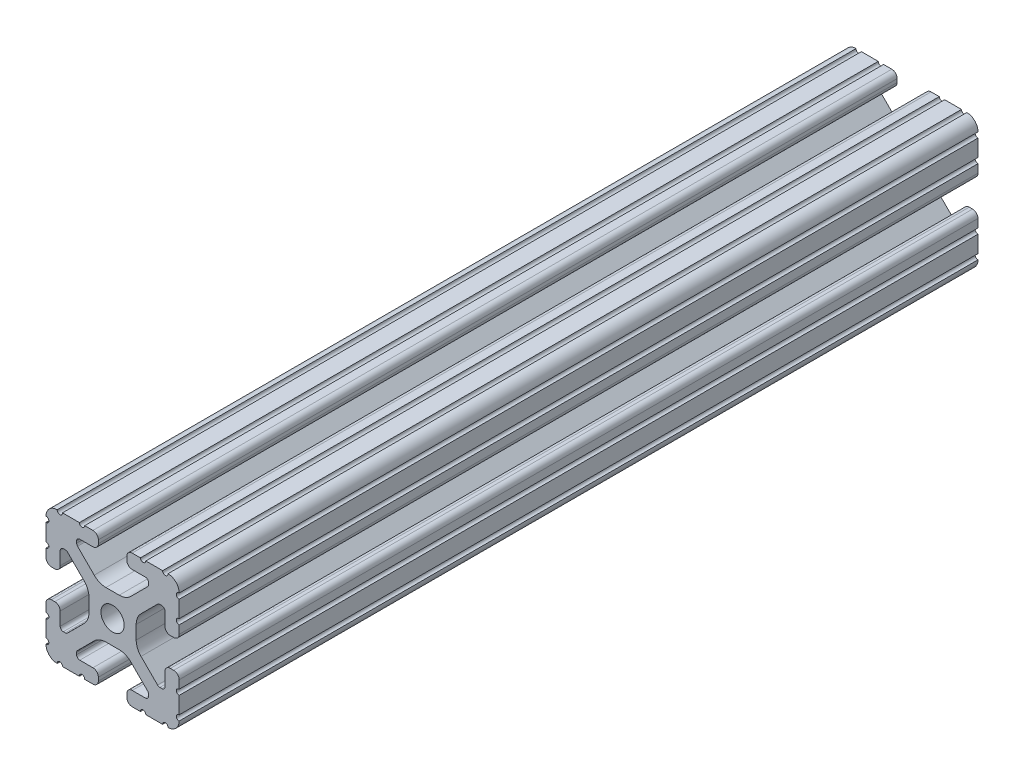
SolidWorks part; units mm, degrees
ref_plane "Front Plane" through (0, 0, 0) normal (0, 0, 1) x (1, 0, 0)
ref_plane "Top Plane" through (0, 0, 0) normal (0, 1, 0) x (1, 0, 0)
ref_plane "Right Plane" through (0, 0, 0) normal (1, 0, 0) x (0, 0, -1)
sketch "Sketch1" plane through (0, 0, 0) normal (0, 0, 1) x (1, 0, 0)
  line L0 (-4.064, 19.05) -> (-4.064, -19.05) construction
  line L1 (-19.05, -19.05) -> (19.05, -19.05) construction
  line L2 (-19.05, -19.05) -> (-19.05, 19.05) construction
  line L3 (-19.05, 19.05) -> (19.05, 19.05) construction
  line L4 (19.05, -19.05) -> (19.05, 19.05) construction
  line L5 (0, 19.05) -> (0, -19.05) construction
  line L6 (-19.05, 0) -> (19.05, 0) construction
  line L7 (-4.064, -19.05) -> (4.064, 19.05) construction
  line L8 (4.064, 19.05) -> (4.064, -19.05) construction
  circle A0 centre (0, 0) radius 3.3274
  point P0 (0, 0)
  line B0 (-10.287, 13.5524) -> (-10.287, 14.0843)
  line B1 (-9.3853, 14.986) -> (-5.6176, 14.986)
  line B2 (-4.064, 16.5396) -> (-4.064, 17.4964)
  line B3 (-5.6176, 19.05) -> (-7.9742, 19.05)
  line B4 (-9.4982, 19.05) -> (-14.3277, 19.05)
  line B5 (-19.05, 14.3277) -> (-19.05, 9.4961)
  line B6 (-19.05, 7.9763) -> (-19.05, 5.6176)
  line B7 (-17.4964, 4.064) -> (-16.5396, 4.064)
  line B8 (-14.986, 5.6176) -> (-14.986, 9.3853)
  line B9 (-14.0843, 10.287) -> (-13.516, 10.287)
  line B10 (-12.8784, 10.0229) -> (-8.1476, 5.2921)
  line B11 (-6.7564, 1.9335) -> (-6.7564, -1.9335)
  line B12 (-8.1476, -5.2921) -> (-12.8784, -10.0229)
  line B13 (-13.516, -10.287) -> (-14.0843, -10.287)
  line B14 (-14.986, -9.3853) -> (-14.986, -5.6176)
  line B15 (-16.5396, -4.064) -> (-17.4964, -4.064)
  line B16 (-19.05, -5.6176) -> (-19.05, -7.9763)
  line B17 (-19.05, -9.4961) -> (-19.05, -14.3277)
  line B18 (-14.3277, -19.05) -> (-9.4961, -19.05)
  line B19 (-7.9763, -19.05) -> (-5.6176, -19.05)
  line B20 (-4.064, -17.4964) -> (-4.064, -16.5396)
  line B21 (-5.6176, -14.986) -> (-9.3853, -14.986)
  line B22 (-10.287, -14.0843) -> (-10.287, -13.5524)
  line B23 (-10.0229, -12.9148) -> (-5.2522, -8.144)
  line B24 (-1.9022, -6.7564) -> (1.9022, -6.7564)
  line B25 (5.2522, -8.144) -> (10.0229, -12.9148)
  line B26 (10.287, -13.5524) -> (10.287, -14.0843)
  line B27 (9.3853, -14.986) -> (5.6176, -14.986)
  line B28 (4.064, -16.5396) -> (4.064, -17.4964)
  line B29 (5.6176, -19.05) -> (7.9763, -19.05)
  line B30 (9.4961, -19.05) -> (14.3277, -19.05)
  line B31 (19.05, -14.3277) -> (19.05, -9.4961)
  line B32 (19.05, -7.9763) -> (19.05, -5.6176)
  line B33 (17.4964, -4.064) -> (16.5396, -4.064)
  line B34 (14.986, -5.6176) -> (14.986, -9.3853)
  line B35 (14.0843, -10.287) -> (13.516, -10.287)
  line B36 (12.8784, -10.0229) -> (8.1476, -5.2921)
  line B37 (6.7564, -1.9335) -> (6.7564, 1.9335)
  line B38 (8.1476, 5.2921) -> (12.8784, 10.0229)
  line B39 (13.516, 10.287) -> (14.0843, 10.287)
  line B40 (14.986, 9.3853) -> (14.986, 5.6176)
  line B41 (16.5396, 4.064) -> (17.4964, 4.064)
  line B42 (19.05, 5.6176) -> (19.05, 7.9763)
  line B43 (19.05, 9.4961) -> (19.05, 14.3277)
  line B44 (14.3277, 19.05) -> (9.4982, 19.05)
  line B45 (7.9742, 19.05) -> (5.6176, 19.05)
  line B46 (4.064, 17.4964) -> (4.064, 16.5396)
  line B47 (5.6176, 14.986) -> (9.3853, 14.986)
  line B48 (10.287, 14.0843) -> (10.287, 13.5524)
  line B49 (10.0229, 12.9148) -> (5.2522, 8.144)
  line B50 (1.9022, 6.7564) -> (-1.9022, 6.7564)
  line B51 (-5.2522, 8.144) -> (-10.0229, 12.9148)
  circle B52 centre (0, 0) radius 3.3274
  arc B53 (-5.6176, 14.986) -> (-4.064, 16.5396) centre (-5.6176, 16.5396) ccw
  arc B54 (-4.064, 17.4964) -> (-5.6176, 19.05) centre (-5.6176, 17.4964) ccw
  arc B55 (-9.4982, 19.05) -> (-7.9742, 19.05) centre (-8.7362, 19.05) ccw
  arc B56 (-15.8475, 19.05) -> (-14.3277, 19.05) centre (-15.0876, 18.9933) ccw
  arc B57 (-15.8475, 19.05) -> (-19.05, 15.8475) centre (-15.8751, 15.8751) ccw
  arc B58 (-19.05, 14.3277) -> (-19.05, 15.8475) centre (-18.9933, 15.0876) ccw
  arc B59 (-19.05, 7.9763) -> (-19.05, 9.4961) centre (-18.9933, 8.7362) ccw
  arc B60 (-19.05, 5.6176) -> (-17.4964, 4.064) centre (-17.4964, 5.6176) ccw
  arc B61 (-16.5396, 4.064) -> (-14.986, 5.6176) centre (-16.5396, 5.6176) ccw
  arc B62 (-14.0843, 10.287) -> (-14.986, 9.3853) centre (-14.0843, 9.3853) ccw
  arc B63 (-12.8784, 10.0229) -> (-13.516, 10.287) centre (-13.516, 9.3853) ccw
  arc B64 (-6.7564, 1.9335) -> (-8.1476, 5.2921) centre (-11.5062, 1.9335) ccw
  arc B65 (-8.1476, -5.2921) -> (-6.7564, -1.9335) centre (-11.5062, -1.9335) ccw
  arc B66 (-13.516, -10.287) -> (-12.8784, -10.0229) centre (-13.516, -9.3853) ccw
  arc B67 (-14.986, -9.3853) -> (-14.0843, -10.287) centre (-14.0843, -9.3853) ccw
  arc B68 (-14.986, -5.6176) -> (-16.5396, -4.064) centre (-16.5396, -5.6176) ccw
  arc B69 (-17.4964, -4.064) -> (-19.05, -5.6176) centre (-17.4964, -5.6176) ccw
  arc B70 (-19.05, -9.4961) -> (-19.05, -7.9763) centre (-18.9933, -8.7362) ccw
  arc B71 (-19.05, -15.8475) -> (-19.05, -14.3277) centre (-18.9933, -15.0876) ccw
  arc B72 (-19.05, -15.8475) -> (-15.8475, -19.05) centre (-15.8751, -15.8751) ccw
  arc B73 (-14.3277, -19.05) -> (-15.8475, -19.05) centre (-15.0876, -18.9933) ccw
  arc B74 (-7.9763, -19.05) -> (-9.4961, -19.05) centre (-8.7362, -18.9933) ccw
  arc B75 (-5.6176, -19.05) -> (-4.064, -17.4964) centre (-5.6176, -17.4964) ccw
  arc B76 (-4.064, -16.5396) -> (-5.6176, -14.986) centre (-5.6176, -16.5396) ccw
  arc B77 (-10.287, -14.0843) -> (-9.3853, -14.986) centre (-9.3853, -14.0843) ccw
  arc B78 (-10.0229, -12.9148) -> (-10.287, -13.5524) centre (-9.3853, -13.5524) ccw
  arc B79 (-1.9022, -6.7564) -> (-5.2522, -8.144) centre (-1.9022, -11.494) ccw
  arc B80 (5.2522, -8.144) -> (1.9022, -6.7564) centre (1.9022, -11.494) ccw
  arc B81 (10.287, -13.5524) -> (10.0229, -12.9148) centre (9.3853, -13.5524) ccw
  arc B82 (9.3853, -14.986) -> (10.287, -14.0843) centre (9.3853, -14.0843) ccw
  arc B83 (5.6176, -14.986) -> (4.064, -16.5396) centre (5.6176, -16.5396) ccw
  arc B84 (4.064, -17.4964) -> (5.6176, -19.05) centre (5.6176, -17.4964) ccw
  arc B85 (9.4961, -19.05) -> (7.9763, -19.05) centre (8.7362, -18.9933) ccw
  arc B86 (15.8475, -19.05) -> (14.3277, -19.05) centre (15.0876, -18.9933) ccw
  arc B87 (15.8475, -19.05) -> (19.05, -15.8475) centre (15.8751, -15.8751) ccw
  arc B88 (19.05, -14.3277) -> (19.05, -15.8475) centre (18.9933, -15.0876) ccw
  arc B89 (19.05, -7.9763) -> (19.05, -9.4961) centre (18.9933, -8.7362) ccw
  arc B90 (19.05, -5.6176) -> (17.4964, -4.064) centre (17.4964, -5.6176) ccw
  arc B91 (16.5396, -4.064) -> (14.986, -5.6176) centre (16.5396, -5.6176) ccw
  arc B92 (14.0843, -10.287) -> (14.986, -9.3853) centre (14.0843, -9.3853) ccw
  arc B93 (12.8784, -10.0229) -> (13.516, -10.287) centre (13.516, -9.3853) ccw
  arc B94 (6.7564, -1.9335) -> (8.1476, -5.2921) centre (11.5062, -1.9335) ccw
  arc B95 (8.1476, 5.2921) -> (6.7564, 1.9335) centre (11.5062, 1.9335) ccw
  arc B96 (13.516, 10.287) -> (12.8784, 10.0229) centre (13.516, 9.3853) ccw
  arc B97 (14.986, 9.3853) -> (14.0843, 10.287) centre (14.0843, 9.3853) ccw
  arc B98 (14.986, 5.6176) -> (16.5396, 4.064) centre (16.5396, 5.6176) ccw
  arc B99 (17.4964, 4.064) -> (19.05, 5.6176) centre (17.4964, 5.6176) ccw
  arc B100 (19.05, 9.4961) -> (19.05, 7.9763) centre (18.9933, 8.7362) ccw
  arc B101 (19.05, 15.8475) -> (19.05, 14.3277) centre (18.9933, 15.0876) ccw
  arc B102 (19.05, 15.8475) -> (15.8475, 19.05) centre (15.8751, 15.8751) ccw
  arc B103 (14.3277, 19.05) -> (15.8475, 19.05) centre (15.0876, 18.9933) ccw
  arc B104 (7.9742, 19.05) -> (9.4982, 19.05) centre (8.7362, 19.05) ccw
  arc B105 (5.6176, 19.05) -> (4.064, 17.4964) centre (5.6176, 17.4964) ccw
  arc B106 (4.064, 16.5396) -> (5.6176, 14.986) centre (5.6176, 16.5396) ccw
  arc B107 (10.287, 14.0843) -> (9.3853, 14.986) centre (9.3853, 14.0843) ccw
  arc B108 (10.0229, 12.9148) -> (10.287, 13.5524) centre (9.3853, 13.5524) ccw
  arc B109 (1.9022, 6.7564) -> (5.2522, 8.144) centre (1.9022, 11.494) ccw
  arc B110 (-5.2522, 8.144) -> (-1.9022, 6.7564) centre (-1.9022, 11.494) ccw
  arc B111 (-10.287, 13.5524) -> (-10.0229, 12.9148) centre (-9.3853, 13.5524) ccw
  dimension "Center Hole Diameter" = 6.6548
  dimension "Rail Width" = 38.1
  dimension "Rail Height" = 38.1
  dimension "T-Slot Width" = 8.128
sketch_block_instance "Block1-1"
sketch_block "Block1"
sketch "Sketch2" plane through (0, 0, 0) normal (1, 0, 0) x (0, 0, -1)
  line L0 (-457.2, 0) -> (457.2, 0) construction
  line L1 (-406.4, 0) -> (-406.4, 19.05) construction
  line L2 (-406.4, 19.05) -> (406.4, 19.05) construction
  line L3 (406.4, 19.05) -> (406.4, 0) construction
  dimension "D1" = 50.8
  dimension "Length" = 914.4
sketch "Sketch3" plane through (0, 0, 0) normal (0, 0, 1) x (1, 0, 0)
  line L0 (-4.064, 16.5396) -> (-4.064, 17.4964) construction
  line L1 (-9.3853, 14.986) -> (-5.6176, 14.986) construction
  line L2 (-10.287, 13.5524) -> (-10.287, 14.0843) construction
  line L3 (-5.2522, 8.144) -> (-10.0229, 12.9148) construction
  line L4 (1.9022, 6.7564) -> (-1.9022, 6.7564) construction
  line L5 (10.0229, 12.9148) -> (5.2522, 8.144) construction
  line L6 (10.287, 14.0843) -> (10.287, 13.5524) construction
  line L7 (5.6176, 14.986) -> (9.3853, 14.986) construction
  line L8 (4.064, 17.4964) -> (4.064, 16.5396) construction
  line L9 (7.9742, 19.05) -> (5.6176, 19.05) construction
  line L10 (14.3277, 19.05) -> (9.4982, 19.05) construction
  line L11 (19.05, 9.4961) -> (19.05, 14.3277) construction
  line L12 (19.05, 5.6176) -> (19.05, 7.9763) construction
  line L13 (16.5396, 4.064) -> (17.4964, 4.064) construction
  line L14 (14.986, 9.3853) -> (14.986, 5.6176) construction
  line L15 (13.516, 10.287) -> (14.0843, 10.287) construction
  line L16 (8.1476, 5.2921) -> (12.8784, 10.0229) construction
  line L17 (6.7564, -1.9335) -> (6.7564, 1.9335) construction
  line L18 (12.8784, -10.0229) -> (8.1476, -5.2921) construction
  line L19 (14.0843, -10.287) -> (13.516, -10.287) construction
  line L20 (14.986, -5.6176) -> (14.986, -9.3853) construction
  line L21 (17.4964, -4.064) -> (16.5396, -4.064) construction
  line L22 (19.05, -7.9763) -> (19.05, -5.6176) construction
  line L23 (19.05, -14.3277) -> (19.05, -9.4961) construction
  line L24 (9.4961, -19.05) -> (14.3277, -19.05) construction
  line L25 (5.6176, -19.05) -> (7.9763, -19.05) construction
  line L26 (4.064, -16.5396) -> (4.064, -17.4964) construction
  line L27 (9.3853, -14.986) -> (5.6176, -14.986) construction
  line L28 (10.287, -13.5524) -> (10.287, -14.0843) construction
  line L29 (5.2522, -8.144) -> (10.0229, -12.9148) construction
  line L30 (-1.9022, -6.7564) -> (1.9022, -6.7564) construction
  line L31 (-10.0229, -12.9148) -> (-5.2522, -8.144) construction
  line L32 (-10.287, -14.0843) -> (-10.287, -13.5524) construction
  line L33 (-5.6176, -14.986) -> (-9.3853, -14.986) construction
  line L34 (-4.064, -17.4964) -> (-4.064, -16.5396) construction
  line L35 (-7.9763, -19.05) -> (-5.6176, -19.05) construction
  line L36 (-14.3277, -19.05) -> (-9.4961, -19.05) construction
  line L37 (-19.05, -9.4961) -> (-19.05, -14.3277) construction
  line L38 (-19.05, -5.6176) -> (-19.05, -7.9763) construction
  line L39 (-16.5396, -4.064) -> (-17.4964, -4.064) construction
  line L40 (-14.986, -9.3853) -> (-14.986, -5.6176) construction
  line L41 (-13.516, -10.287) -> (-14.0843, -10.287) construction
  line L42 (-8.1476, -5.2921) -> (-12.8784, -10.0229) construction
  line L43 (-6.7564, 1.9335) -> (-6.7564, -1.9335) construction
  line L44 (-12.8784, 10.0229) -> (-8.1476, 5.2921) construction
  line L45 (-14.0843, 10.287) -> (-13.516, 10.287) construction
  line L46 (-14.986, 5.6176) -> (-14.986, 9.3853) construction
  line L47 (-17.4964, 4.064) -> (-16.5396, 4.064) construction
  line L48 (-19.05, 7.9763) -> (-19.05, 5.6176) construction
  line L49 (-19.05, 14.3277) -> (-19.05, 9.4961) construction
  line L50 (-9.4982, 19.05) -> (-14.3277, 19.05) construction
  line L51 (-5.6176, 19.05) -> (-7.9742, 19.05) construction
  line L52 (-4.064, 16.5396) -> (-4.064, 17.4964)
  line L53 (-9.3853, 14.986) -> (-5.6176, 14.986)
  line L54 (-10.287, 13.5524) -> (-10.287, 14.0843)
  line L55 (-5.2522, 8.144) -> (-10.0229, 12.9148)
  line L56 (1.9022, 6.7564) -> (-1.9022, 6.7564)
  line L57 (10.0229, 12.9148) -> (5.2522, 8.144)
  line L58 (10.287, 14.0843) -> (10.287, 13.5524)
  line L59 (5.6176, 14.986) -> (9.3853, 14.986)
  line L60 (4.064, 17.4964) -> (4.064, 16.5396)
  line L61 (7.9742, 19.05) -> (5.6176, 19.05)
  line L62 (14.3277, 19.05) -> (9.4982, 19.05)
  line L63 (19.05, 9.4961) -> (19.05, 14.3277)
  line L64 (19.05, 5.6176) -> (19.05, 7.9763)
  line L65 (16.5396, 4.064) -> (17.4964, 4.064)
  line L66 (14.986, 9.3853) -> (14.986, 5.6176)
  line L67 (13.516, 10.287) -> (14.0843, 10.287)
  line L68 (8.1476, 5.2921) -> (12.8784, 10.0229)
  line L69 (6.7564, -1.9335) -> (6.7564, 1.9335)
  line L70 (12.8784, -10.0229) -> (8.1476, -5.2921)
  line L71 (14.0843, -10.287) -> (13.516, -10.287)
  line L72 (14.986, -5.6176) -> (14.986, -9.3853)
  line L73 (17.4964, -4.064) -> (16.5396, -4.064)
  line L74 (19.05, -7.9763) -> (19.05, -5.6176)
  line L75 (19.05, -14.3277) -> (19.05, -9.4961)
  line L76 (9.4961, -19.05) -> (14.3277, -19.05)
  line L77 (5.6176, -19.05) -> (7.9763, -19.05)
  line L78 (4.064, -16.5396) -> (4.064, -17.4964)
  line L79 (9.3853, -14.986) -> (5.6176, -14.986)
  line L80 (10.287, -13.5524) -> (10.287, -14.0843)
  line L81 (5.2522, -8.144) -> (10.0229, -12.9148)
  line L82 (-1.9022, -6.7564) -> (1.9022, -6.7564)
  line L83 (-10.0229, -12.9148) -> (-5.2522, -8.144)
  line L84 (-10.287, -14.0843) -> (-10.287, -13.5524)
  line L85 (-5.6176, -14.986) -> (-9.3853, -14.986)
  line L86 (-4.064, -17.4964) -> (-4.064, -16.5396)
  line L87 (-7.9763, -19.05) -> (-5.6176, -19.05)
  line L88 (-14.3277, -19.05) -> (-9.4961, -19.05)
  line L89 (-19.05, -9.4961) -> (-19.05, -14.3277)
  line L90 (-19.05, -5.6176) -> (-19.05, -7.9763)
  line L91 (-16.5396, -4.064) -> (-17.4964, -4.064)
  line L92 (-14.986, -9.3853) -> (-14.986, -5.6176)
  line L93 (-13.516, -10.287) -> (-14.0843, -10.287)
  line L94 (-8.1476, -5.2921) -> (-12.8784, -10.0229)
  line L95 (-6.7564, 1.9335) -> (-6.7564, -1.9335)
  line L96 (-12.8784, 10.0229) -> (-8.1476, 5.2921)
  line L97 (-14.0843, 10.287) -> (-13.516, 10.287)
  line L98 (-14.986, 5.6176) -> (-14.986, 9.3853)
  line L99 (-17.4964, 4.064) -> (-16.5396, 4.064)
  line L100 (-19.05, 7.9763) -> (-19.05, 5.6176)
  line L101 (-19.05, 14.3277) -> (-19.05, 9.4961)
  line L102 (-9.4982, 19.05) -> (-14.3277, 19.05)
  line L103 (-5.6176, 19.05) -> (-7.9742, 19.05)
  circle A0 centre (0, 0) radius 3.3274 construction
  circle A1 centre (0, 0) radius 3.3274
  circle A2 centre (0, 0) radius 3.3274
  arc A3 (-5.6176, 14.986) -> (-4.064, 16.5396) centre (-5.6176, 16.5396) ccw construction
  arc A4 (-9.3853, 14.986) -> (-10.287, 14.0843) centre (-9.3853, 14.0843) ccw construction
  arc A5 (-10.287, 13.5524) -> (-10.0229, 12.9148) centre (-9.3853, 13.5524) ccw construction
  arc A6 (-5.2522, 8.144) -> (-1.9022, 6.7564) centre (-1.9022, 11.494) ccw construction
  arc A7 (1.9022, 6.7564) -> (5.2522, 8.144) centre (1.9022, 11.494) ccw construction
  arc A8 (10.0229, 12.9148) -> (10.287, 13.5524) centre (9.3853, 13.5524) ccw construction
  arc A9 (10.287, 14.0843) -> (9.3853, 14.986) centre (9.3853, 14.0843) ccw construction
  arc A10 (4.064, 16.5396) -> (5.6176, 14.986) centre (5.6176, 16.5396) ccw construction
  arc A11 (5.6176, 19.05) -> (4.064, 17.4964) centre (5.6176, 17.4964) ccw construction
  arc A12 (7.9742, 19.05) -> (9.4982, 19.05) centre (8.7362, 19.05) ccw construction
  arc A13 (14.3277, 19.05) -> (15.8475, 19.05) centre (15.0876, 18.9933) ccw construction
  arc A14 (19.05, 15.8475) -> (15.8475, 19.05) centre (15.8751, 15.8751) ccw construction
  arc A15 (19.05, 15.8475) -> (19.05, 14.3277) centre (18.9933, 15.0876) ccw construction
  arc A16 (19.05, 9.4961) -> (19.05, 7.9763) centre (18.9933, 8.7362) ccw construction
  arc A17 (17.4964, 4.064) -> (19.05, 5.6176) centre (17.4964, 5.6176) ccw construction
  arc A18 (14.986, 5.6176) -> (16.5396, 4.064) centre (16.5396, 5.6176) ccw construction
  arc A19 (14.986, 9.3853) -> (14.0843, 10.287) centre (14.0843, 9.3853) ccw construction
  arc A20 (13.516, 10.287) -> (12.8784, 10.0229) centre (13.516, 9.3853) ccw construction
  arc A21 (8.1476, 5.2921) -> (6.7564, 1.9335) centre (11.5062, 1.9335) ccw construction
  arc A22 (6.7564, -1.9335) -> (8.1476, -5.2921) centre (11.5062, -1.9335) ccw construction
  arc A23 (12.8784, -10.0229) -> (13.516, -10.287) centre (13.516, -9.3853) ccw construction
  arc A24 (14.0843, -10.287) -> (14.986, -9.3853) centre (14.0843, -9.3853) ccw construction
  arc A25 (16.5396, -4.064) -> (14.986, -5.6176) centre (16.5396, -5.6176) ccw construction
  arc A26 (19.05, -5.6176) -> (17.4964, -4.064) centre (17.4964, -5.6176) ccw construction
  arc A27 (19.05, -7.9763) -> (19.05, -9.4961) centre (18.9933, -8.7362) ccw construction
  arc A28 (19.05, -14.3277) -> (19.05, -15.8475) centre (18.9933, -15.0876) ccw construction
  arc A29 (15.8475, -19.05) -> (19.05, -15.8475) centre (15.8751, -15.8751) ccw construction
  arc A30 (15.8475, -19.05) -> (14.3277, -19.05) centre (15.0876, -18.9933) ccw construction
  arc A31 (9.4961, -19.05) -> (7.9763, -19.05) centre (8.7362, -18.9933) ccw construction
  arc A32 (4.064, -17.4964) -> (5.6176, -19.05) centre (5.6176, -17.4964) ccw construction
  arc A33 (5.6176, -14.986) -> (4.064, -16.5396) centre (5.6176, -16.5396) ccw construction
  arc A34 (9.3853, -14.986) -> (10.287, -14.0843) centre (9.3853, -14.0843) ccw construction
  arc A35 (10.287, -13.5524) -> (10.0229, -12.9148) centre (9.3853, -13.5524) ccw construction
  arc A36 (5.2522, -8.144) -> (1.9022, -6.7564) centre (1.9022, -11.494) ccw construction
  arc A37 (-1.9022, -6.7564) -> (-5.2522, -8.144) centre (-1.9022, -11.494) ccw construction
  arc A38 (-10.0229, -12.9148) -> (-10.287, -13.5524) centre (-9.3853, -13.5524) ccw construction
  arc A39 (-10.287, -14.0843) -> (-9.3853, -14.986) centre (-9.3853, -14.0843) ccw construction
  arc A40 (-4.064, -16.5396) -> (-5.6176, -14.986) centre (-5.6176, -16.5396) ccw construction
  arc A41 (-5.6176, -19.05) -> (-4.064, -17.4964) centre (-5.6176, -17.4964) ccw construction
  arc A42 (-7.9763, -19.05) -> (-9.4961, -19.05) centre (-8.7362, -18.9933) ccw construction
  arc A43 (-14.3277, -19.05) -> (-15.8475, -19.05) centre (-15.0876, -18.9933) ccw construction
  arc A44 (-19.05, -15.8475) -> (-15.8475, -19.05) centre (-15.8751, -15.8751) ccw construction
  arc A45 (-19.05, -15.8475) -> (-19.05, -14.3277) centre (-18.9933, -15.0876) ccw construction
  arc A46 (-19.05, -9.4961) -> (-19.05, -7.9763) centre (-18.9933, -8.7362) ccw construction
  arc A47 (-17.4964, -4.064) -> (-19.05, -5.6176) centre (-17.4964, -5.6176) ccw construction
  arc A48 (-14.986, -5.6176) -> (-16.5396, -4.064) centre (-16.5396, -5.6176) ccw construction
  arc A49 (-14.986, -9.3853) -> (-14.0843, -10.287) centre (-14.0843, -9.3853) ccw construction
  arc A50 (-13.516, -10.287) -> (-12.8784, -10.0229) centre (-13.516, -9.3853) ccw construction
  arc A51 (-8.1476, -5.2921) -> (-6.7564, -1.9335) centre (-11.5062, -1.9335) ccw construction
  arc A52 (-6.7564, 1.9335) -> (-8.1476, 5.2921) centre (-11.5062, 1.9335) ccw construction
  arc A53 (-12.8784, 10.0229) -> (-13.516, 10.287) centre (-13.516, 9.3853) ccw construction
  arc A54 (-14.0843, 10.287) -> (-14.986, 9.3853) centre (-14.0843, 9.3853) ccw construction
  arc A55 (-16.5396, 4.064) -> (-14.986, 5.6176) centre (-16.5396, 5.6176) ccw construction
  arc A56 (-19.05, 5.6176) -> (-17.4964, 4.064) centre (-17.4964, 5.6176) ccw construction
  arc A57 (-19.05, 7.9763) -> (-19.05, 9.4961) centre (-18.9933, 8.7362) ccw construction
  arc A58 (-19.05, 14.3277) -> (-19.05, 15.8475) centre (-18.9933, 15.0876) ccw construction
  arc A59 (-15.8475, 19.05) -> (-19.05, 15.8475) centre (-15.8751, 15.8751) ccw construction
  arc A60 (-15.8475, 19.05) -> (-14.3277, 19.05) centre (-15.0876, 18.9933) ccw construction
  arc A61 (-9.4982, 19.05) -> (-7.9742, 19.05) centre (-8.7362, 19.05) ccw construction
  arc A62 (-4.064, 17.4964) -> (-5.6176, 19.05) centre (-5.6176, 17.4964) ccw construction
  circle A63 centre (0, 0) radius 3.3274
  arc A64 (-5.6176, 14.986) -> (-4.064, 16.5396) centre (-5.6176, 16.5396) ccw
  arc A65 (-9.3853, 14.986) -> (-10.287, 14.0843) centre (-9.3853, 14.0843) ccw
  arc A66 (-10.287, 13.5524) -> (-10.0229, 12.9148) centre (-9.3853, 13.5524) ccw
  arc A67 (-5.2522, 8.144) -> (-1.9022, 6.7564) centre (-1.9022, 11.494) ccw
  arc A68 (1.9022, 6.7564) -> (5.2522, 8.144) centre (1.9022, 11.494) ccw
  arc A69 (10.0229, 12.9148) -> (10.287, 13.5524) centre (9.3853, 13.5524) ccw
  arc A70 (10.287, 14.0843) -> (9.3853, 14.986) centre (9.3853, 14.0843) ccw
  arc A71 (4.064, 16.5396) -> (5.6176, 14.986) centre (5.6176, 16.5396) ccw
  arc A72 (5.6176, 19.05) -> (4.064, 17.4964) centre (5.6176, 17.4964) ccw
  arc A73 (7.9742, 19.05) -> (9.4982, 19.05) centre (8.7362, 19.05) ccw
  arc A74 (14.3277, 19.05) -> (15.8475, 19.05) centre (15.0876, 18.9933) ccw
  arc A75 (19.05, 15.8475) -> (15.8475, 19.05) centre (15.8751, 15.8751) ccw
  arc A76 (19.05, 15.8475) -> (19.05, 14.3277) centre (18.9933, 15.0876) ccw
  arc A77 (19.05, 9.4961) -> (19.05, 7.9763) centre (18.9933, 8.7362) ccw
  arc A78 (17.4964, 4.064) -> (19.05, 5.6176) centre (17.4964, 5.6176) ccw
  arc A79 (14.986, 5.6176) -> (16.5396, 4.064) centre (16.5396, 5.6176) ccw
  arc A80 (14.986, 9.3853) -> (14.0843, 10.287) centre (14.0843, 9.3853) ccw
  arc A81 (13.516, 10.287) -> (12.8784, 10.0229) centre (13.516, 9.3853) ccw
  arc A82 (8.1476, 5.2921) -> (6.7564, 1.9335) centre (11.5062, 1.9335) ccw
  arc A83 (6.7564, -1.9335) -> (8.1476, -5.2921) centre (11.5062, -1.9335) ccw
  arc A84 (12.8784, -10.0229) -> (13.516, -10.287) centre (13.516, -9.3853) ccw
  arc A85 (14.0843, -10.287) -> (14.986, -9.3853) centre (14.0843, -9.3853) ccw
  arc A86 (16.5396, -4.064) -> (14.986, -5.6176) centre (16.5396, -5.6176) ccw
  arc A87 (19.05, -5.6176) -> (17.4964, -4.064) centre (17.4964, -5.6176) ccw
  arc A88 (19.05, -7.9763) -> (19.05, -9.4961) centre (18.9933, -8.7362) ccw
  arc A89 (19.05, -14.3277) -> (19.05, -15.8475) centre (18.9933, -15.0876) ccw
  arc A90 (15.8475, -19.05) -> (19.05, -15.8475) centre (15.8751, -15.8751) ccw
  arc A91 (15.8475, -19.05) -> (14.3277, -19.05) centre (15.0876, -18.9933) ccw
  arc A92 (9.4961, -19.05) -> (7.9763, -19.05) centre (8.7362, -18.9933) ccw
  arc A93 (4.064, -17.4964) -> (5.6176, -19.05) centre (5.6176, -17.4964) ccw
  arc A94 (5.6176, -14.986) -> (4.064, -16.5396) centre (5.6176, -16.5396) ccw
  arc A95 (9.3853, -14.986) -> (10.287, -14.0843) centre (9.3853, -14.0843) ccw
  arc A96 (10.287, -13.5524) -> (10.0229, -12.9148) centre (9.3853, -13.5524) ccw
  arc A97 (5.2522, -8.144) -> (1.9022, -6.7564) centre (1.9022, -11.494) ccw
  arc A98 (-1.9022, -6.7564) -> (-5.2522, -8.144) centre (-1.9022, -11.494) ccw
  arc A99 (-10.0229, -12.9148) -> (-10.287, -13.5524) centre (-9.3853, -13.5524) ccw
  arc A100 (-10.287, -14.0843) -> (-9.3853, -14.986) centre (-9.3853, -14.0843) ccw
  arc A101 (-4.064, -16.5396) -> (-5.6176, -14.986) centre (-5.6176, -16.5396) ccw
  arc A102 (-5.6176, -19.05) -> (-4.064, -17.4964) centre (-5.6176, -17.4964) ccw
  arc A103 (-7.9763, -19.05) -> (-9.4961, -19.05) centre (-8.7362, -18.9933) ccw
  arc A104 (-14.3277, -19.05) -> (-15.8475, -19.05) centre (-15.0876, -18.9933) ccw
  arc A105 (-19.05, -15.8475) -> (-15.8475, -19.05) centre (-15.8751, -15.8751) ccw
  arc A106 (-19.05, -15.8475) -> (-19.05, -14.3277) centre (-18.9933, -15.0876) ccw
  arc A107 (-19.05, -9.4961) -> (-19.05, -7.9763) centre (-18.9933, -8.7362) ccw
  arc A108 (-17.4964, -4.064) -> (-19.05, -5.6176) centre (-17.4964, -5.6176) ccw
  arc A109 (-14.986, -5.6176) -> (-16.5396, -4.064) centre (-16.5396, -5.6176) ccw
  arc A110 (-14.986, -9.3853) -> (-14.0843, -10.287) centre (-14.0843, -9.3853) ccw
  arc A111 (-13.516, -10.287) -> (-12.8784, -10.0229) centre (-13.516, -9.3853) ccw
  arc A112 (-8.1476, -5.2921) -> (-6.7564, -1.9335) centre (-11.5062, -1.9335) ccw
  arc A113 (-6.7564, 1.9335) -> (-8.1476, 5.2921) centre (-11.5062, 1.9335) ccw
  arc A114 (-12.8784, 10.0229) -> (-13.516, 10.287) centre (-13.516, 9.3853) ccw
  arc A115 (-14.0843, 10.287) -> (-14.986, 9.3853) centre (-14.0843, 9.3853) ccw
  arc A116 (-16.5396, 4.064) -> (-14.986, 5.6176) centre (-16.5396, 5.6176) ccw
  arc A117 (-19.05, 5.6176) -> (-17.4964, 4.064) centre (-17.4964, 5.6176) ccw
  arc A118 (-19.05, 7.9763) -> (-19.05, 9.4961) centre (-18.9933, 8.7362) ccw
  arc A119 (-19.05, 14.3277) -> (-19.05, 15.8475) centre (-18.9933, 15.0876) ccw
  arc A120 (-15.8475, 19.05) -> (-19.05, 15.8475) centre (-15.8751, 15.8751) ccw
  arc A121 (-15.8475, 19.05) -> (-14.3277, 19.05) centre (-15.0876, 18.9933) ccw
  arc A122 (-9.4982, 19.05) -> (-7.9742, 19.05) centre (-8.7362, 19.05) ccw
  arc A123 (-4.064, 17.4964) -> (-5.6176, 19.05) centre (-5.6176, 17.4964) ccw
  dimension "D1" = 0
extrude "Boss-Extrude1" add sketch "Sketch3" along normal up to vertex (457.2 mm away) and the other way up to vertex (457.2 mm away) contours L52 A123 L103 A122 L102 A121 A120 A119 L101 A118 L100 A117 L99 A116 L98 A115 L97 A114 L96 A113 L95 A112 L94 A111 L93 A110 L92 A109 L91 A108 L90 A107 L89 A106 A105 A104 L88 A103 L87 A102 L86 A101 L85 A100 L84 A99 L83 A98 L82 A97 L81 up to point (0, 0, 457.2) other way up to point (0, 0, -457.2)
sketch "Sketch4" plane through (0, 0, 0) normal (0, 1, 0) x (1, 0, 0)
  line L0 (-11.9129, 457.2) -> (-11.9129, 228.6) construction
  line L1 (-9.4982, 457.2) -> (-14.3277, 457.2) construction
  line L9 (-11.9129, 228.6) -> (-26.026, 228.6)
  line L10 (-26.026, 228.6) -> (-26.026, -478.3735)
  line L11 (-26.026, -478.3735) -> (32.6353, -478.3735)
  line L12 (32.6353, -478.3735) -> (32.6353, 228.6)
  line L13 (32.6353, 228.6) -> (-11.9129, 228.6)
extrude "Cut-Extrude1" cut sketch "Sketch4" against normal mid plane 45.72
